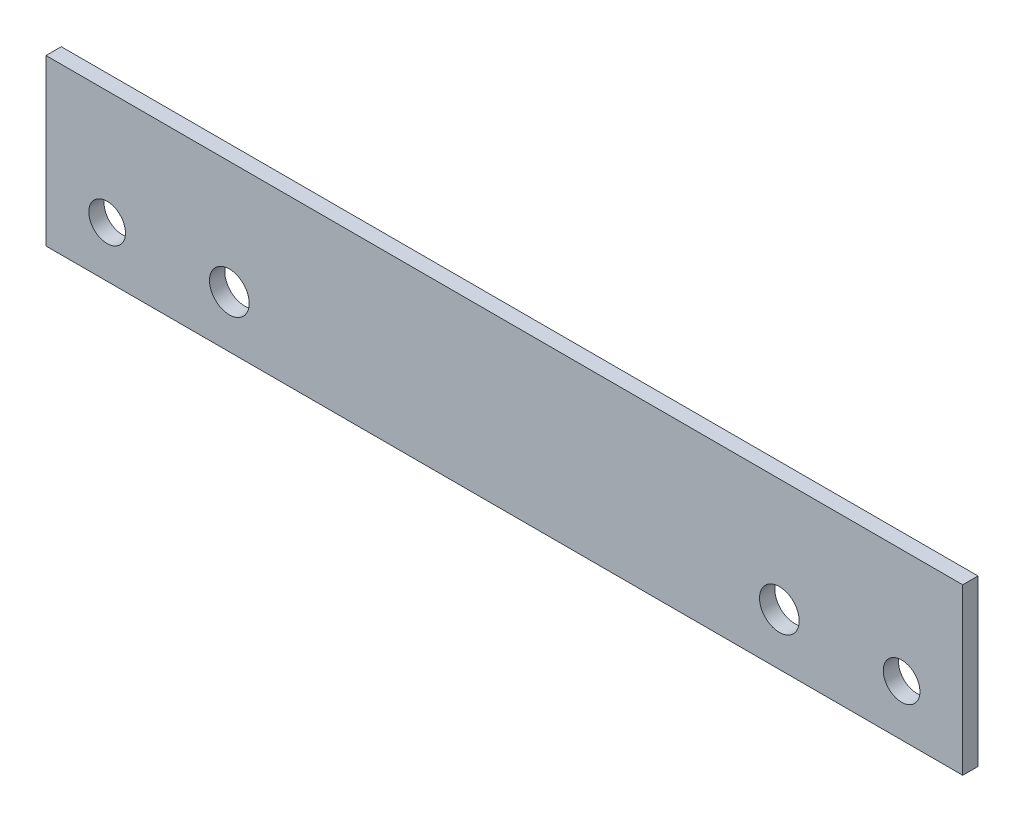
SolidWorks part; units mm, degrees
ref_plane "前视基准面" through (0, 0, 0) normal (0, 0, 1) x (1, 0, 0)
ref_plane "上视基准面" through (0, 0, 0) normal (0, 1, 0) x (1, 0, 0)
ref_plane "右视基准面" through (0, 0, 0) normal (1, 0, 0) x (0, 0, -1)
sketch "草图1" plane through (0, 0, 0) normal (0, 0, 1) x (1, 0, 0)
  line L1 (-150, -27) -> (150, -27)
  line L2 (-150, -27) -> (-150, 27)
  line L3 (-150, 27) -> (150, 27)
  line L4 (150, -27) -> (150, 27)
  line L5 (-150, -27) -> (150, 27) construction
  line L6 (-150, 27) -> (150, -27) construction
  point P0 (0, 0)
  dimension "D1" = 300
  dimension "D2" = 54
extrude "凸台-拉伸1" add sketch "草图1" along normal blind 5
sketch "草图2" plane through (0, 0, 0) normal (0, 0, -1) x (-1, 0, 0)
  line L0 (150, -27) -> (-150, -27) construction
  line L1 (-150, -27) -> (-150, 27) construction
  circle A0 centre (-130, -10.3) radius 6
  dimension "D3" = 12
  dimension "D1" = 16.7
  dimension "D2" = 20
extrude "切除-拉伸1" cut sketch "草图2" against normal through all
mirror "镜向1" about plane through (0, 0, 0) normal (1, 0, 0) of "切除-拉伸1"
sketch "草图3" plane through (0, 0, 0) normal (0, 0, -1) x (-1, 0, 0)
  line L0 (0, 0) -> (0, 72.1895) construction
  line L1 (-150, -27) -> (-150, 27) construction
  line L3 (150, -27) -> (-150, -27) construction
  circle A0 centre (-90, -10) radius 6.5
  dimension "D1" = 13
  dimension "D3" = 17
  dimension "D2" = 60
extrude "切除-拉伸2" cut sketch "草图3" against normal blind 10
mirror "镜向2" about plane through (0, 0, 0) normal (1, 0, 0) of "切除-拉伸2"
